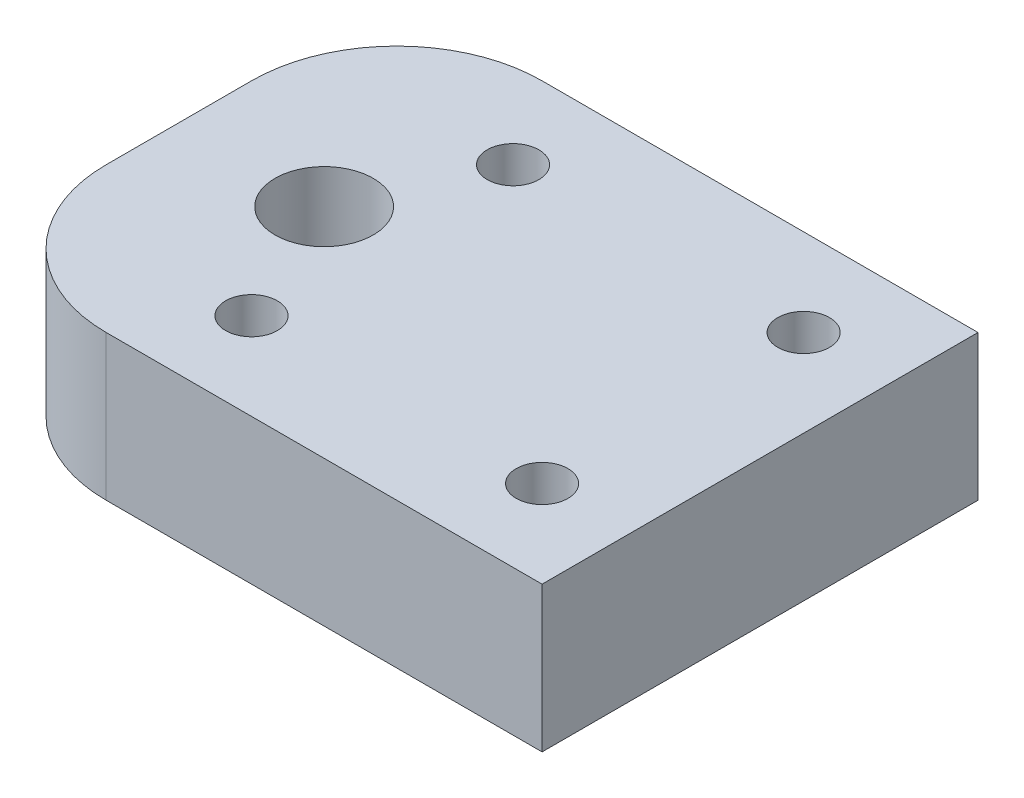
SolidWorks part; units mm, degrees
material "Acrylic (BLUE)"
ref_plane "Front Plane" through (0, 0, 0) normal (0, 0, 1) x (1, 0, 0)
ref_plane "Top Plane" through (0, 0, 0) normal (0, 1, 0) x (1, 0, 0)
ref_plane "Right Plane" through (0, 0, 0) normal (1, 0, 0) x (0, 0, -1)
sketch "Sketch1" plane through (0, 0, 0) normal (0, 1, 0) x (1, 0, 0)
  line L0 (0, 0) -> (-6.35, 0) construction
  line L1 (-6.35, 9.525) -> (19.05, 9.525)
  line L2 (-6.35, 9.525) -> (-6.35, -9.525)
  line L3 (-6.35, -9.525) -> (19.05, -9.525)
  line L4 (19.05, 9.525) -> (19.05, -9.525)
  line L5 (6.35, 3.175) -> (19.05, 3.175) construction
  line L6 (6.35, 3.175) -> (6.35, -3.175) construction
  line L7 (19.05, -3.175) -> (6.35, -3.175) construction
  line L8 (0, 0) -> (6.35, 0) construction
  line L10 (6.35, 3.175) -> (4.445, 3.175) construction
  line L11 (6.35, 3.175) -> (6.35, -3.175) construction
  line L12 (6.35, -3.175) -> (4.445, -3.175) construction
  line L13 (4.445, 3.175) -> (4.445, -3.175) construction
  circle A0 centre (0, 0) radius 2.1463
  dimension "D1" = 4.2926
  dimension "D2" = 19.05
  dimension "D3" = 6.35
  dimension "D4" = 6.35
  dimension "D5" = 25.4
  dimension "D6" = 12.7
  dimension "D7" = 1.905
extrude "Boss-Extrude1" add sketch "Sketch1" along normal blind 6.35
hole_wizard "#4-40 Tapped Hole1" positions "Sketch4" profile "Sketch5" tap size "#4-40" standard "ANSI Inch"
sketch "Sketch4" plane through (0, 6.35, 0) normal (0, 1, 0) x (1, 0, 0)
  line L1 (2.54, 5.715) -> (15.24, 5.715)
  line L2 (2.54, 5.715) -> (2.54, -5.715)
  line L3 (2.54, -5.715) -> (15.24, -5.715)
  line L4 (15.24, 5.715) -> (15.24, -5.715)
  line L5 (0, 0) -> (2.54, 0) construction
  line L7 (-6.35, 9.525) -> (-6.35, -9.525) construction
  point P0 (2.54, 5.715)
  point P1 (15.24, -5.715)
  point P122 (2.54, -5.715)
  point P123 (15.24, 5.715)
  dimension "D1" = 8.89
  dimension "D2" = 12.7
  dimension "D3" = 11.43
sketch "Sketch5" plane through (2.54, 6.35, -5.715) normal (1, 0, 0) x (0, 0, 1)
  line L0 (0, 0) -> (0, 8.2738)
  line L1 (0, 8.2738) -> (1.1303, 7.5946)
  line L2 (1.1303, 7.5946) -> (1.1303, 0)
  line L5 (1.1303, 0) -> (0, 0)
  line L10 (0, 8.2738) -> (-1.1303, 7.5946) construction
  line L11 (0, -6.35) -> (0, 107.95) construction
  dimension "Tap Drill Dia." = 2.2606
  dimension "Tap Drill Depth" = 7.5946
  dimension "Drill Angle" = 118
fillet "Fillet1" radius 6.35 2 edges at (-6.35, 3.175, -9.525) (-6.35, 3.175, 9.525)
